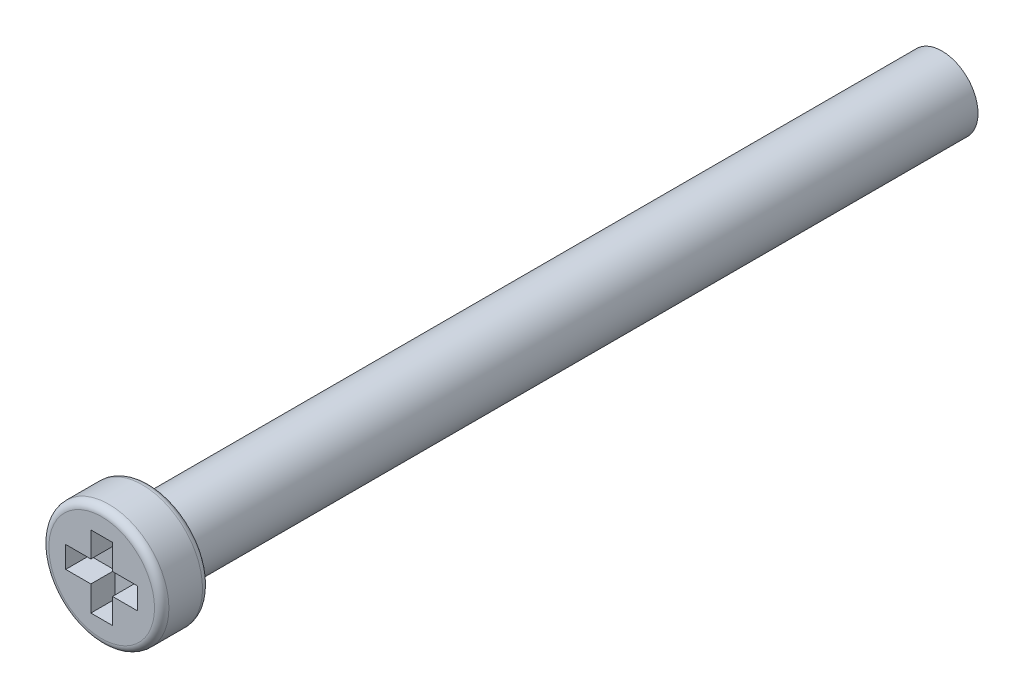
SolidWorks part; units mm, degrees
material "Ст. 3кп ГОСТ 380-2005"
ref_plane "Спереди" through (0, 0, 0) normal (0, 0, 1) x (1, 0, 0)
ref_plane "Сверху" through (0, 0, 0) normal (0, 1, 0) x (1, 0, 0)
ref_plane "Справа" through (0, 0, 0) normal (1, 0, 0) x (0, 0, -1)
sketch "Эскиз1" plane through (0, 0, 0) normal (0, 0, 1) x (1, 0, 0)
  circle A0 centre (0, 0) radius 2.5
  dimension "D1" = 5
extrude "Бобышка-Вытянуть1" add sketch "Эскиз1" along normal blind 2
sketch "Эскиз2" plane through (0, 0, 0) normal (0, 0, -1) x (-1, 0, 0)
  circle A0 centre (0, 0) radius 1.5
  dimension "D1" = 3
extrude "Бобышка-Вытянуть2" add sketch "Эскиз2" along normal blind 33
cosmetic thread "Условное изображение резьбы1" parameters "D1"=32, "D2"=2.439
fillet "Скругление2" radius 0.3 2 edges at (2.5, 0, 0) (2.5, 0, 2)
sketch "Эскиз3" plane through (0, 0, 2) normal (0, 0, 1) x (1, 0, 0)
  line L1 (-0.45, 1.5) -> (0.45, 1.5)
  line L2 (-0.45, 1.5) -> (-0.45, 0.45)
  line L3 (-0.45, -1.5) -> (0.45, -1.5)
  line L4 (0.45, 1.5) -> (0.45, 0.45)
  line L5 (-0.45, 1.5) -> (0.45, -1.5) construction
  line L6 (-0.45, -1.5) -> (0.45, 1.5) construction
  line L7 (-1.5, 0.45) -> (-0.45, 0.45)
  line L8 (-1.5, 0.45) -> (-1.5, -0.45)
  line L9 (-1.5, -0.45) -> (-0.45, -0.45)
  line L10 (1.5, 0.45) -> (1.5, -0.45)
  line L11 (-1.5, 0.45) -> (1.5, -0.45) construction
  line L12 (-1.5, -0.45) -> (1.5, 0.45) construction
  line L13 (0.45, 0.45) -> (1.5, 0.45)
  line L14 (0.45, -0.45) -> (0.45, -1.5)
  line L15 (0.45, -0.45) -> (1.5, -0.45)
  line L16 (-0.45, -0.45) -> (-0.45, -1.5)
  point P0 (0, 0)
  point P6 (0, 0)
  dimension "D1" = 0.9
  dimension "D2" = 3
extrude "Вырез-Вытянуть1" cut sketch "Эскиз3" against normal blind 1
fillet "Скругление1" radius 0.1 1 edges at (1.5, 0, 0)
